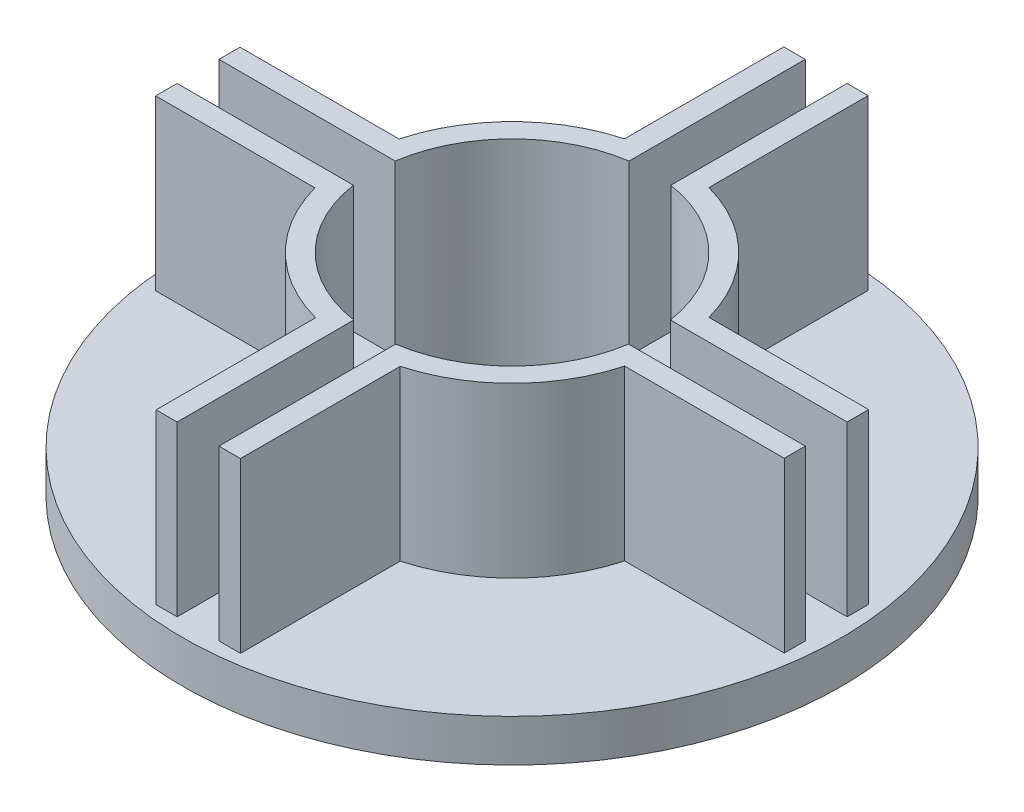
SolidWorks part; units mm, degrees
ref_plane "Front Plane" through (0, 0, 0) normal (0, 0, 1) x (1, 0, 0)
ref_plane "Top Plane" through (0, 0, 0) normal (0, 1, 0) x (1, 0, 0)
ref_plane "Right Plane" through (0, 0, 0) normal (1, 0, 0) x (0, 0, -1)
sketch "Sketch1" plane through (0, 0, 0) normal (0, 1, 0) x (1, 0, 0)
  circle A0 centre (0, 0) radius 21.4312
  circle A1 centre (0, 0) radius 24.13
extrude "Boss-Extrude1" add sketch "Sketch1" along normal blind 25.4
sketch "Sketch2" plane through (0, 0, 0) normal (0, 0, 1) x (1, 0, 0)
  line L0 (-3.1115, 0) -> (3.1115, 0)
  line L1 (3.1115, 0) -> (3.1115, 31.9146)
  line L2 (3.1115, 31.9146) -> (-3.1115, 31.9146)
  line L3 (-3.1115, 31.9146) -> (-3.1115, 0)
  point P4 (0, 0)
extrude "Cut-Extrude1" cut sketch "Sketch2" against normal blind 25.4
pattern_circular "CirPattern1" count 4 over 360 about axis through (0, 0, 0) along (0, 1, 0) of "Cut-Extrude1"
sketch "Sketch3" plane through (0, 0, 0) normal (0, -1, 0) x (1, 0, 0)
  circle A0 centre (0, 0) radius 24.13
  circle A1 centre (0, 0) radius 21.4312
extrude "Boss-Extrude3" add sketch "Sketch3" along normal blind 3.175
sketch "Sketch4" plane through (0, -3.175, 0) normal (0, -1, 0) x (-1, 0, 0)
  circle A0 centre (0, 0) radius 49.6094
  circle A1 centre (0, 0) radius 24.13
extrude "Boss-Extrude4" add sketch "Sketch4" against normal blind 3.175
sketch "Sketch6" plane through (0, 0, 0) normal (0, 1, 0) x (1, 0, 0)
  line L0 (3.1115, 23.9296) -> (6.35, 23.9296) construction
  line L2 (3.1115, 21.2042) -> (3.1115, 23.9296)
  line L5 (3.1115, 21.2042) -> (6.35, 22.1278)
  line L6 (6.35, 22.1278) -> (6.35, 47.2495)
  line L7 (6.35, 47.2495) -> (3.1115, 47.2495)
  line L8 (3.1115, 47.2495) -> (3.1115, 23.9296)
  line L9 (0, 0) -> (0, 50000) construction
  line L10 (-3.1115, 21.2042) -> (-3.1115, 23.9296)
  line L11 (-3.1115, 21.2042) -> (-6.35, 22.1278)
  line L12 (-6.35, 22.1278) -> (-6.35, 47.2495)
  line L13 (-6.35, 47.2495) -> (-3.1115, 47.2495)
  line L14 (-3.1115, 47.2495) -> (-3.1115, 23.9296)
  line L15 (21.2677, 3.1209) -> (23.9931, 3.1209)
  line L16 (47.313, 3.1209) -> (23.9931, 3.1209)
  line L17 (47.313, 6.3594) -> (47.313, 3.1209)
  line L18 (22.1913, 6.3594) -> (47.313, 6.3594)
  line L19 (21.2677, 3.1209) -> (22.1913, 6.3594)
  line L20 (47.313, -3.1021) -> (23.9931, -3.1021)
  line L21 (47.313, -6.3406) -> (47.313, -3.1021)
  line L22 (22.1913, -6.3406) -> (47.313, -6.3406)
  line L23 (21.2677, -3.1021) -> (22.1913, -6.3406)
  line L24 (21.2677, -3.1021) -> (23.9931, -3.1021)
  line L25 (3.1844, -21.2583) -> (3.1844, -23.9837)
  line L26 (3.1844, -47.3036) -> (3.1844, -23.9837)
  line L27 (6.4229, -47.3036) -> (3.1844, -47.3036)
  line L28 (6.4229, -22.1819) -> (6.4229, -47.3036)
  line L29 (3.1844, -21.2583) -> (6.4229, -22.1819)
  line L30 (-3.0386, -47.3036) -> (-3.0386, -23.9837)
  line L31 (-6.2771, -47.3036) -> (-3.0386, -47.3036)
  line L32 (-6.2771, -22.1819) -> (-6.2771, -47.3036)
  line L33 (-3.0386, -21.2583) -> (-6.2771, -22.1819)
  line L34 (-3.0386, -21.2583) -> (-3.0386, -23.9837)
  line L35 (-21.1948, -3.175) -> (-23.9202, -3.175)
  line L36 (-47.2401, -3.175) -> (-23.9202, -3.175)
  line L37 (-47.2401, -6.4135) -> (-47.2401, -3.175)
  line L38 (-22.1184, -6.4135) -> (-47.2401, -6.4135)
  line L39 (-21.1948, -3.175) -> (-22.1184, -6.4135)
  line L40 (-47.2401, 3.048) -> (-23.9202, 3.048)
  line L41 (-47.2401, 6.2865) -> (-47.2401, 3.048)
  line L42 (-22.1184, 6.2865) -> (-47.2401, 6.2865)
  line L43 (-21.1948, 3.048) -> (-22.1184, 6.2865)
  line L44 (-21.1948, 3.048) -> (-23.9202, 3.048)
  dimension "D1" = 4
extrude "Boss-Extrude5" add sketch "Sketch6" along normal up to surface (25.4 mm away) up to face at (-14.4736, 25.4, -14.4736)
sketch "Sketch11" plane through (0, -3.175, 0) normal (0, -1, 0) x (1, 0, 0)
  circle A0 centre (0, 0) radius 21.4312
  circle A1 centre (0, 0) radius 20.955
extrude "Boss-Extrude6" add sketch "Sketch11" against normal up to surface (28.575 mm away)
sketch "Sketch14" plane through (0, -3.175, 0) normal (0, -1, 0) x (1, 0, 0)
  circle A0 centre (0, 0) radius 20.955
  circle A1 centre (0, 0) radius 49.6094
extrude "Boss-Extrude7" add sketch "Sketch14" along normal blind 3.175
sketch "Sketch15" plane through (0, 25.4, 0) normal (0, 1, 0) x (1, 0, 0)
  line L1 (47.313, 3.1209) -> (-47.2401, 3.1209)
  line L2 (47.313, 3.1209) -> (47.313, -3.175)
  line L3 (47.313, -3.175) -> (-47.2401, -3.175)
  line L4 (-47.2401, 3.1209) -> (-47.2401, -3.175)
extrude "Cut-Extrude8" cut sketch "Sketch15" against normal up to surface (25.4 mm away) up to face at (-21.2081, 0, -3.1048)
sketch "Sketch16" plane through (0, 25.4, 0) normal (0, 1, 0) x (1, 0, 0)
  line L1 (-3.1115, 47.2495) -> (3.1844, 47.2495)
  line L2 (-3.1115, 47.2495) -> (-3.1115, -47.3036)
  line L3 (-3.1115, -47.3036) -> (3.1844, -47.3036)
  line L4 (3.1844, 47.2495) -> (3.1844, -47.3036)
extrude "Cut-Extrude9" cut sketch "Sketch16" against normal up to surface (25.4 mm away) up to face at (0.0238, 0, 2.5283)
